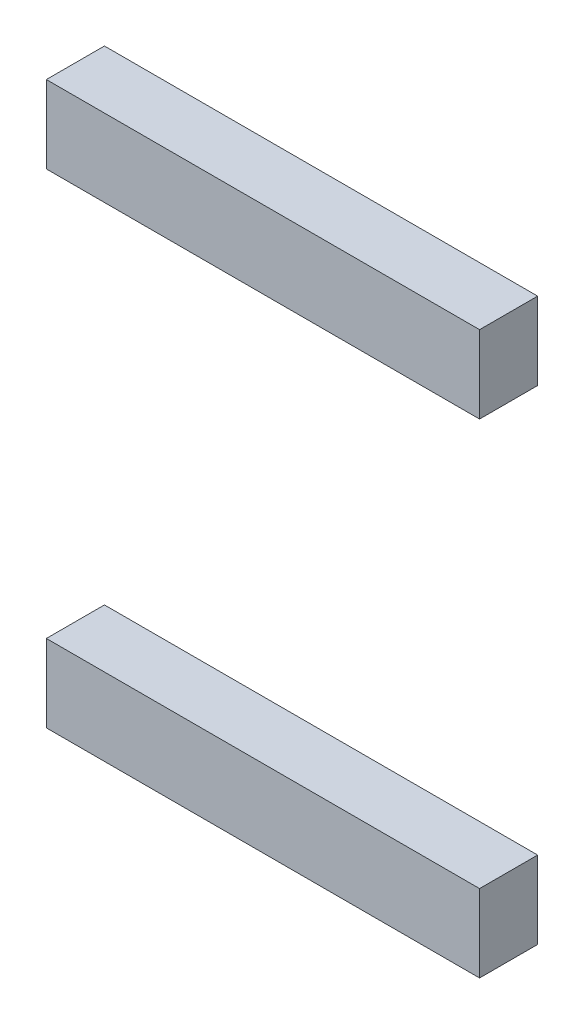
SolidWorks part; units mm, degrees
ref_plane "Front Plane" through (0, 0, 0) normal (0, 0, 1) x (1, 0, 0)
ref_plane "Top Plane" through (0, 0, 0) normal (0, 1, 0) x (1, 0, 0)
ref_plane "Right Plane" through (0, 0, 0) normal (1, 0, 0) x (0, 0, -1)
sketch "Sketch2" plane through (0, 0, 0) normal (0, 0, 1) x (-1, 0, 0)
  line L0 (0.375, -31.5) -> (22.75, -31.5)
  line L1 (0.375, -6.5) -> (22.75, -6.5)
  line L2 (0.375, -6.5) -> (0.375, -10.5)
  line L3 (0.375, -10.5) -> (22.75, -10.5)
  line L4 (22.75, -6.5) -> (22.75, -10.5)
  line L5 (0.375, -31.5) -> (0.375, -35.5)
  line L6 (0.375, -35.5) -> (22.75, -35.5)
  line L7 (22.75, -31.5) -> (22.75, -35.5)
  dimension "D1" = 2
extrude "Boss-Extrude1" add sketch "Sketch2" along normal blind 3
